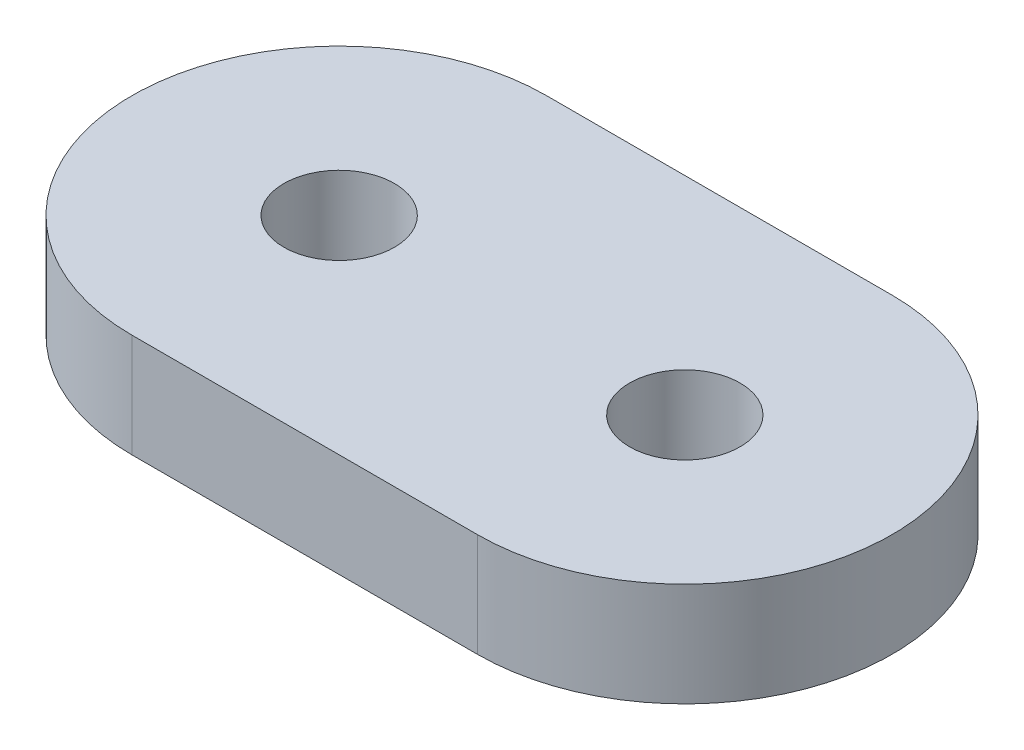
SolidWorks part; units mm, degrees
material "Thornel VCB-20 Carbon Cloth"
ref_plane "Front Plane" through (0, 0, 0) normal (0, 0, 1) x (1, 0, 0)
ref_plane "Top Plane" through (0, 0, 0) normal (0, 1, 0) x (1, 0, 0)
ref_plane "Right Plane" through (0, 0, 0) normal (1, 0, 0) x (0, 0, -1)
sketch "Sketch1" plane through (0, 0, 0) normal (0, 1, 0) x (1, 0, 0)
  line L0 (-5, 0) -> (5, 0) construction
  line L1 (-5, 6) -> (5, 6)
  line L2 (-5, -6) -> (5, -6)
  arc A0 (-5, 6) -> (-5, -6) centre (-5, 0) ccw
  arc A1 (5, -6) -> (5, 6) centre (5, 0) ccw
  point P3 (0, 0)
  dimension "D2" = 6
  dimension "D1" = 10
extrude "Boss-Extrude1" add sketch "Sketch1" along normal mid plane 3
hole_wizard "M3 Clearance Hole1" positions "Sketch2" profile "Sketch3" hole size "M3" standard "ANSI Metric" end condition up to next
sketch "Sketch2" plane through (0, 1.5, 0) normal (0, 1, 0) x (1, 0, 0)
  point P0 (-5, 0)
  point P3 (5, 0)
sketch "Sketch3" plane through (-5, 1.5, 0) normal (1, 0, 0) x (0, 0, 1)
  line L0 (0, 0) -> (0, 3)
  line L1 (0, 3) -> (1.6, 3)
  line L2 (1.6, 3) -> (1.6, 0)
  line L5 (1.6, 0) -> (0, 0)
  line L11 (0, -6.35) -> (0, 107.95) construction
  dimension "Thru Hole Dia." = 3.2
  dimension "Thru Hole Depth" = 3
